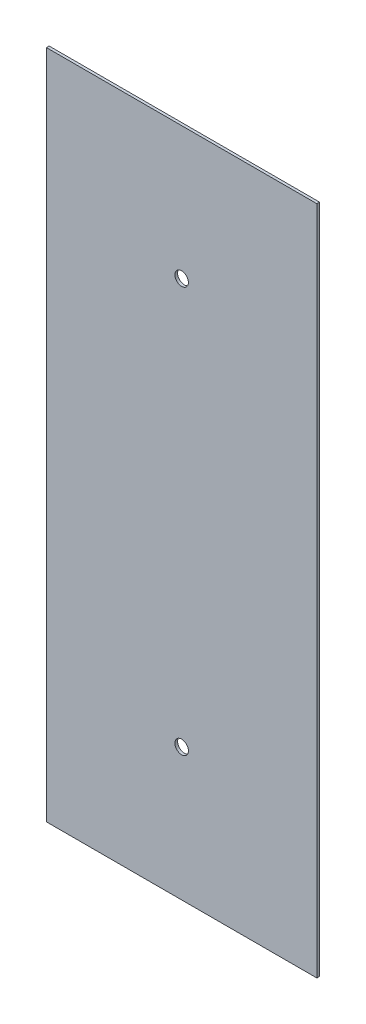
SolidWorks part; units mm, degrees
material "Plain Carbon Steel"
ref_plane "Front Plane" through (0, 0, 0) normal (0, 0, 1) x (1, 0, 0)
ref_plane "Top Plane" through (0, 0, 0) normal (0, 1, 0) x (1, 0, 0)
ref_plane "Right Plane" through (0, 0, 0) normal (1, 0, 0) x (0, 0, -1)
sketch "Sketch1" plane through (0, 0, 0) normal (0, 0, 1) x (1, 0, 0)
  line L0 (0, 150) -> (0, -150) construction
  line L1 (100, 248) -> (-100, 248)
  line L2 (100, 248) -> (100, -248)
  line L3 (100, -248) -> (-100, -248)
  line L4 (-100, 248) -> (-100, -248)
  line L5 (100, 248) -> (-100, -248) construction
  line L6 (100, -248) -> (-100, 248) construction
  circle A0 centre (0, 150) radius 5
  circle A1 centre (0, -150) radius 5
  point P0 (0, 0)
  point P9 (0, 0)
  dimension "D4" = 10
  dimension "D1" = 200
  dimension "D2" = 496
  dimension "D3" = 300
extrude "Boss-Extrude1" add sketch "Sketch1" along normal blind 2
